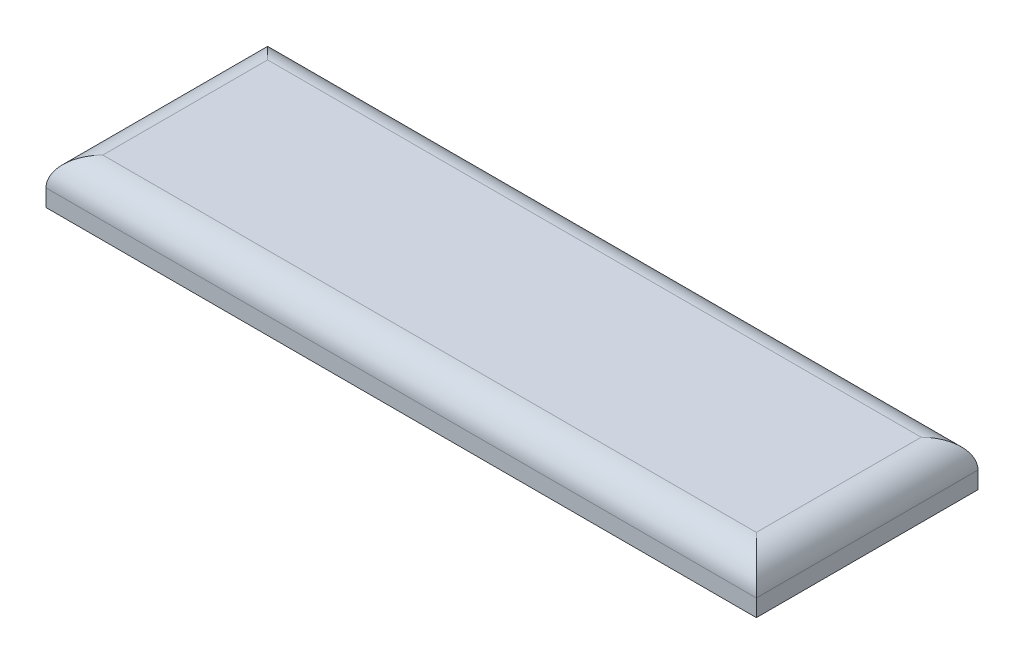
SolidWorks part; units mm, degrees
material "玻璃"
ref_plane "前视基准面" through (0, 0, 0) normal (0, 0, 1) x (1, 0, 0)
ref_plane "上视基准面" through (0, 0, 0) normal (0, 1, 0) x (1, 0, 0)
ref_plane "右视基准面" through (0, 0, 0) normal (1, 0, 0) x (0, 0, -1)
other "Configuration Table"
sketch "草图1" plane through (0, 0, 0) normal (0, 1, 0) x (1, 0, 0)
  line L1 (-12.5, 3.9) -> (12.5, 3.9)
  line L2 (-12.5, 3.9) -> (-12.5, -3.9)
  line L3 (-12.5, -3.9) -> (12.5, -3.9)
  line L4 (12.5, 3.9) -> (12.5, -3.9)
  line L5 (-12.5, 3.9) -> (12.5, -3.9) construction
  line L6 (-12.5, -3.9) -> (12.5, 3.9) construction
  point P0 (0, 0)
  dimension "D1" = 25
  dimension "D2" = 7.8
extrude "凸台-拉伸1" add sketch "草图1" along normal blind 1.6
fillet "圆角1" radius 1 4 edges at (12.5, 1.6, 0) (0, 1.6, 3.9) (0, 1.6, -3.9) (-12.5, 1.6, 0)
